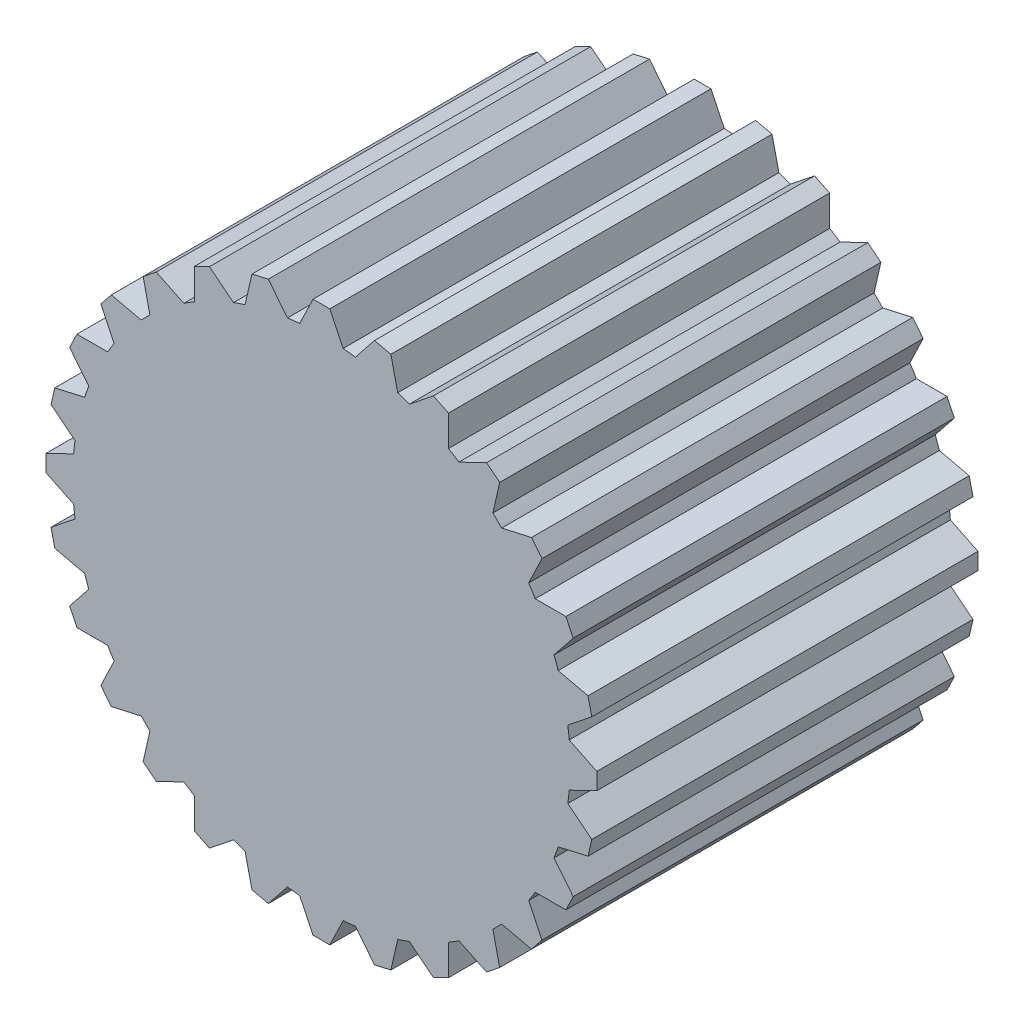
SolidWorks part; units mm, degrees
ref_plane "Front Plane" through (0, 0, 0) normal (0, 0, 1) x (1, 0, 0)
ref_plane "Top Plane" through (0, 0, 0) normal (0, 1, 0) x (1, 0, 0)
ref_plane "Right Plane" through (0, 0, 0) normal (1, 0, 0) x (0, 0, -1)
sketch "Sketch1" plane through (0, 0, 0) normal (0, 0, 1) x (1, 0, 0)
  line L0 (0, 0) -> (0, 7.225)
  line L1 (-0.22, 7.225) -> (0.22, 7.225)
  line L2 (-0.57, 6.5) -> (0.57, 6.5)
  line L3 (0.22, 7.225) -> (0.57, 6.5)
  line L4 (0, 6.5) -> (0, 6.44)
  line L5 (-0.22, 7.225) -> (-0.57, 6.5)
  line L6 (0.57, 6.5) -> (0, 0)
  line L7 (-0.57, 6.5) -> (0, 0)
  circle A0 centre (0, 0) radius 6.5
  circle A1 centre (0, 0) radius 2.8
  circle A2 centre (0, 0) radius 6.5249
  dimension "D1" = 13
  dimension "D2" = 5.6
  dimension "D3" = 7.225
  dimension "D4" = 0.22
  dimension "D5" = 0.57
extrude "Boss-Extrude1" add sketch "Sketch1" along normal blind 10 contours A1 L0 A0 L7 | L0 A1 L7 | A1 L6 A0 L0 | L6 A1 L0 | A2 L3 L1 L0 | A2 L0 L1 L5 | L0 A2 L2 | L2 A2 L0 | A0 L6 L2 | A0 L2 L7
pattern_circular "CirPattern1" count 28 over 360 about axis through (0, 0, 0) along (0, 0, 1) of "Boss-Extrude1"
sketch "Sketch2" plane through (0, 0, 10) normal (0, 0, 1) x (1, 0, 0)
  circle A0 centre (0, 0) radius 6.5249
extrude "Boss-Extrude2" add sketch "Sketch2" against normal blind 10
